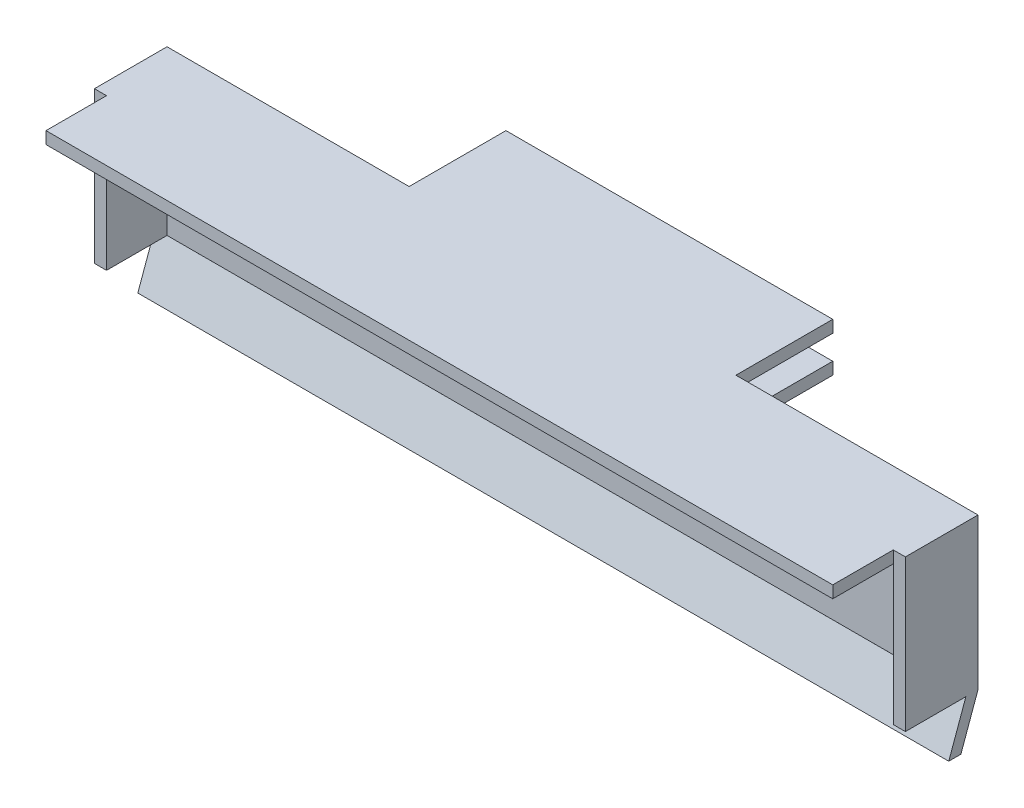
SolidWorks part; units mm, degrees
ref_plane "Alzado" through (0, 0, 0) normal (0, 0, 1) x (1, 0, 0)
ref_plane "Planta" through (0, 0, 0) normal (0, 1, 0) x (1, 0, 0)
ref_plane "Vista lateral" through (0, 0, 0) normal (1, 0, 0) x (0, 0, -1)
sketch "Croquis1" plane through (0, 0, 0) normal (0, 0, 1) x (1, 0, 0)
  line L1 (-73.8306, 17.8824) -> (-8.8306, 17.8824)
  line L2 (-73.8306, 17.8824) -> (-73.8306, 7.3824)
  line L3 (-73.8306, 7.3824) -> (-8.8306, 7.3824)
  line L4 (-8.8306, 17.8824) -> (-8.8306, 7.3824)
  dimension "D1" = 65
  dimension "D2" = 10.5
extrude "Saliente-Extruir1" add sketch "Croquis1" along normal blind 1
sketch "Croquis5" plane through (0, 0, 0) normal (0, 0, -1) x (-1, 0, 0)
  line L1 (8.8306, 17.8824) -> (73.8306, 17.8824)
  line L2 (8.8306, 17.8824) -> (8.8306, 7.3824)
  line L3 (8.8306, 7.3824) -> (73.8306, 7.3824)
  line L4 (73.8306, 17.8824) -> (73.8306, 7.3824)
  line L5 (7.8306, 18.8824) -> (74.8306, 18.8824)
  line L6 (7.8306, 18.8824) -> (7.8306, 6.3824)
  line L7 (7.8306, 6.3824) -> (74.8306, 6.3824)
  line L8 (74.8306, 18.8824) -> (74.8306, 6.3824)
  dimension "D1" = 1
  dimension "D2" = 1
  dimension "D3" = 1
  dimension "D4" = 1
extrude "Saliente-Extruir3" add sketch "Croquis5" against normal blind 6
sketch "Croquis6" plane through (0, 0, 0) normal (0, 0, -1) x (-1, 0, 0)
  line L0 (74.8306, 18.8824) -> (7.8306, 18.8824) construction
  line L1 (27.8306, 18.8824) -> (54.8306, 18.8824)
  line L2 (27.8306, 18.8824) -> (27.8306, 17.8824)
  line L3 (27.8306, 17.8824) -> (54.8306, 17.8824)
  line L4 (54.8306, 18.8824) -> (54.8306, 17.8824)
  line L5 (7.8306, 18.8824) -> (7.8306, 6.3824) construction
  line L6 (74.8306, 6.3824) -> (74.8306, 18.8824) construction
  line L8 (27.8306, 15.8824) -> (54.8306, 15.8824)
  line L9 (27.8306, 15.8824) -> (27.8306, 14.8824)
  line L10 (27.8306, 14.8824) -> (54.8306, 14.8824)
  line L11 (54.8306, 15.8824) -> (54.8306, 14.8824)
  dimension "D1" = 20
  dimension "D2" = 20
  dimension "D3" = 1
  dimension "D4" = 2
  dimension "D5" = 1
extrude "Saliente-Extruir4" add sketch "Croquis6" along normal blind 8
sketch "Croquis7" plane through (0, 0, 6) normal (0, 0, 1) x (1, 0, 0)
  line L0 (-7.8306, 6.3824) -> (-74.8306, 6.3824) construction
  line L1 (-8.8306, 7.3824) -> (-73.8306, 7.3824)
  line L2 (-8.8306, 7.3824) -> (-8.8306, 6.3824)
  line L3 (-8.8306, 6.3824) -> (-73.8306, 6.3824)
  line L4 (-73.8306, 7.3824) -> (-73.8306, 6.3824)
extrude "Cortar-Extruir1" cut sketch "Croquis7" against normal up to vertex (5 mm away)
sketch "Croquis8" plane through (-7.8306, 0, 0) normal (1, 0, 0) x (0, 0, -1)
  line L0 (0, 6.3824) -> (-1.0007, 6.3824)
  line L1 (-6, 6.3824) -> (0, 6.3824) construction
  line L2 (-1.0007, 6.3824) -> (-2.4149, 2.4681)
  line L3 (0, 6.3824) -> (-1.4142, 2.4681)
  line L4 (-1.4142, 2.4681) -> (-2.4149, 2.4681)
extrude "Saliente-Extruir5" add sketch "Croquis8" against normal up to vertex (67 mm away)
sketch "Croquis9" plane through (0, 0, 6) normal (0, 0, 1) x (1, 0, 0)
  line L0 (-74.8306, 18.8824) -> (-7.8306, 18.8824) construction
  line L1 (-8.8306, 17.8824) -> (-73.8306, 17.8824)
  line L2 (-8.8306, 17.8824) -> (-8.8306, 18.8824)
  line L3 (-8.8306, 18.8824) -> (-73.8306, 18.8824)
  line L4 (-73.8306, 17.8824) -> (-73.8306, 18.8824)
extrude "Saliente-Extruir6" add sketch "Croquis9" along normal blind 5
